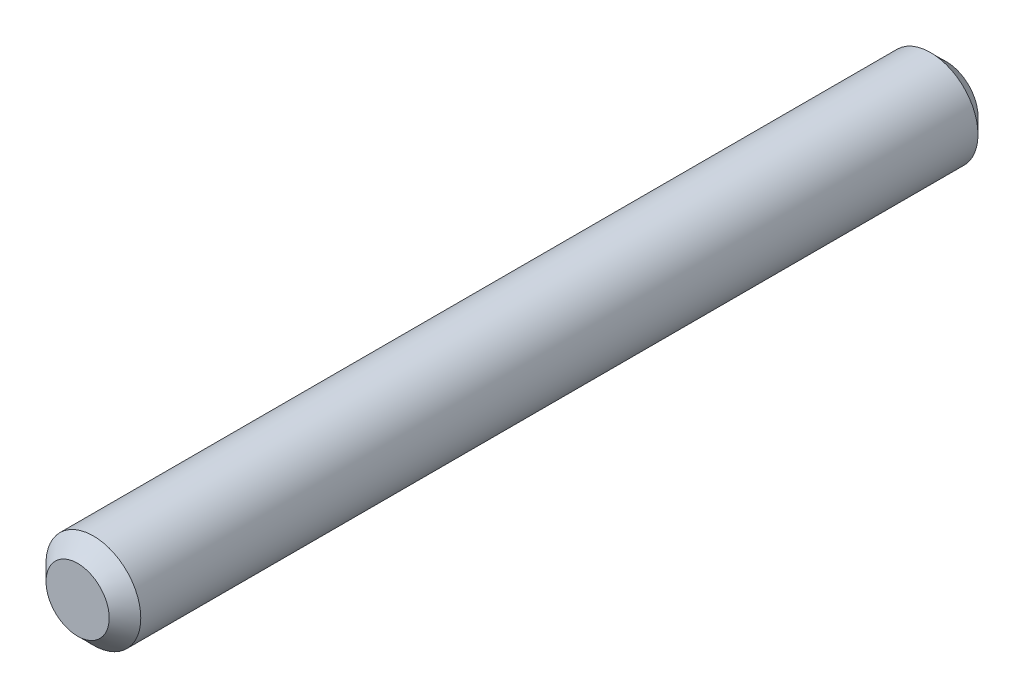
SolidWorks part; units mm, degrees
material "AISI Type 316L stainless steel"
ref_plane "Front Plane" through (0, 0, 0) normal (0, 0, 1) x (1, 0, 0)
ref_plane "Top Plane" through (0, 0, 0) normal (0, 1, 0) x (1, 0, 0)
ref_plane "Right Plane" through (0, 0, 0) normal (1, 0, 0) x (0, 0, -1)
sketch "Sketch1" plane through (0, 0, 0) normal (0, 0, 1) x (1, 0, 0)
  circle A0 centre (0, 0) radius 3
  dimension "D1" = 6
extrude "Boss-Extrude1" add sketch "Sketch1" along normal blind 55
chamfer "Chamfer1" distance 1 angle 45 2 edges at (3, 0, 0) (3, 0, 55)
